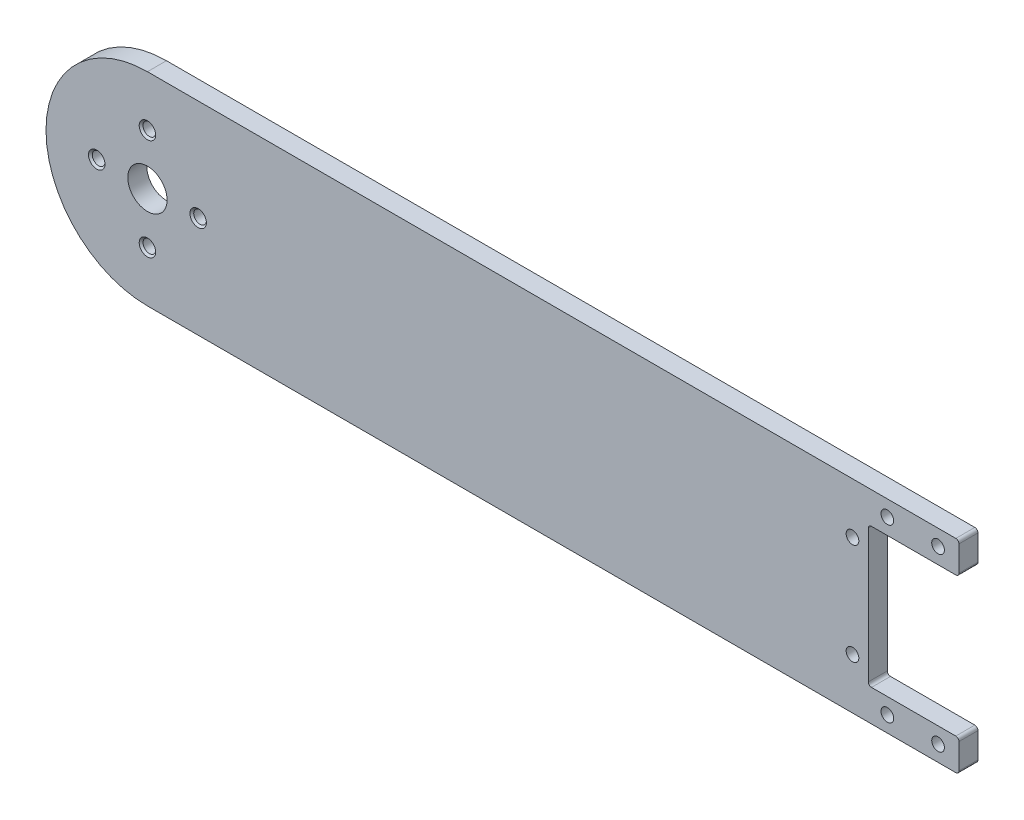
SolidWorks part; units mm, degrees
material "ABS"
ref_plane "Ön Düzlem" through (0, 0, 0) normal (0, 0, 1) x (1, 0, 0)
ref_plane "Üst Düzlem" through (0, 0, 0) normal (0, 1, 0) x (1, 0, 0)
ref_plane "Sağ Düzlem" through (0, 0, 0) normal (1, 0, 0) x (0, 0, -1)
sketch "Çizim1" plane through (0, 0, 0) normal (0, 0, 1) x (1, 0, 0)
  line L0 (-61, -16) -> (59, -16)
  line L1 (-61, 16) -> (59, 16)
  line L3 (59, 16) -> (75, 16)
  line L4 (59, 16) -> (59, -16)
  line L5 (59, -16) -> (75, -16)
  line L6 (75, 16) -> (75, -16)
  arc A0 (59, 16) -> (75, 0) centre (59, 0) cw
  arc A1 (-61, 16) -> (-77, 0) centre (-61, 0) ccw
  circle A2 centre (-61, 0) radius 16
  circle A3 centre (59, 0) radius 16
  point P0 (0, 0)
  dimension "D3" = 16
  dimension "D4" = 32
  dimension "D5" = 32
  dimension "D7" = 16
  dimension "D8" = 61
  dimension "D2" = 120
  dimension "D6" = 120
  dimension "D9" = 16
  dimension "D10" = 32
  dimension "D11" = 16
  dimension "D12" = 152
extrude "Yükseklik-Ekstrüzyon1" add sketch "Çizim1" along normal blind 3 contours A3 L1 A2 L0 | A0 A3 | L4 L3 L6 L5
sketch "Çizim2" plane through (0, 0, 3) normal (0, 0, 1) x (1, 0, 0)
  circle A0 centre (-61, 0) radius 8 construction
  circle A1 centre (-61, 0) radius 3.1
  point P4 (-61, 8)
  point P5 (-53, 0)
  point P6 (-61, -8)
  point P7 (-69, 0)
  dimension "D1" = 16
  dimension "D2" = 6.2
extrude "Kes-Ekstrüzyon1" cut sketch "Çizim2" against normal through all
hole_wizard "M2 Düz Başlı Makine Vidası İçin Havşa1" positions "3B Çizim1" profile "Çizim7" countersink size "M2" standard "ANSI Metrik" end condition through all
sketch3d "3B Çizim1"
  point P0 (-61, 8, 3)
  point P3 (-53, 0, 3)
  point P6 (-61, -8, 3)
  point P9 (-69, 0, 3)
sketch "Çizim7" plane through (-61, 8, 3) normal (1, 0, 0) x (0, -1, 0)
  line L0 (0, 0) -> (0, 3)
  line L1 (0, 3) -> (1, 3)
  line L2 (1, 3) -> (1, 0.3)
  line L3 (1, 0.3) -> (1.3, 0)
  line L5 (1.3, 0) -> (0, 0)
  line L6 (-1, 0.3) -> (-1.3, 0) construction
  line L11 (0, -6.35) -> (0, 107.95) construction
  dimension "Thru Hole Dia." = 2
  dimension "Thru Hole Depth" = 3
  dimension "Near C'Sink Dia." = 2.6
  dimension "Near C'Sink Angle" = 90
sketch "Çizim26" plane through (0, 0, 3) normal (0, 0, 1) x (1, 0, 0)
  line L0 (75, 16) -> (75, -16) construction
  line L1 (75, 11) -> (52.7, 11)
  line L2 (75, 11) -> (75, -11)
  line L3 (75, -11) -> (52.7, -11)
  line L4 (52.7, 11) -> (52.7, -11)
  line L5 (-61, -16) -> (75, -16) construction
  line L6 (-61, 16) -> (75, 16) construction
  point P8 (71.7, 13.5)
  point P9 (63.7, 13.5)
  point P10 (55.7, 13.5)
  point P11 (50.2, 8)
  point P12 (50.2, -8)
  point P13 (55.7, -13.5)
  point P14 (63.7, -13.5)
  point P15 (71.7, -13.5)
  dimension "D1" = 22.3
  dimension "D2" = 22
  dimension "D3" = 5
  dimension "D4" = 8
  dimension "D5" = 8
  dimension "D6" = 8
  dimension "D7" = 8
  dimension "D8" = 2.5
  dimension "D9" = 2.5
  dimension "D10" = 3.3
  dimension "D11" = 3.3
  dimension "D12" = 8
  dimension "D13" = 2.5
  dimension "D14" = 2.5
  dimension "D15" = 8
extrude "Kes-Ekstrüzyon4" cut sketch "Çizim26" against normal through all
sketch "Vida Del. Ref" plane through (0, 0, 0) normal (0, 0, -1) x (-1, 0, 0)
  point P0 (-71.7, 13.5)
  point P1 (-63.7, 13.5)
  point P3 (-55.7, 13.5)
  point P5 (-50.2, 8)
  point P7 (-50.2, -8)
  point P9 (-55.7, -13.5)
  point P11 (-63.7, -13.5)
  point P13 (-71.7, -13.5)
hole_wizard "M2 Düz Başlı Makine Vidası İçin Havşa2" positions "3B Çizim4" profile "Çizim32" countersink size "M2" standard "ANSI Metrik" end condition through all
sketch3d "3B Çizim4"
  point P0 (71.7, 13.5, 0)
  point P3 (63.7, 13.5, 0)
  point P6 (55.7, 13.5, 0)
  point P9 (50.2, 8, 0)
  point P12 (50.2, -8, 0)
  point P15 (55.7, -13.5, 0)
  point P18 (63.7, -13.5, 0)
  point P21 (71.7, -13.5, 0)
sketch "Çizim32" plane through (71.7, 13.5, 0) normal (1, 0, 0) x (0, 1, 0)
  line L0 (0, 0) -> (0, 3)
  line L1 (0, 3) -> (1, 3)
  line L2 (1, 3) -> (1, 0.3)
  line L3 (1, 0.3) -> (1.3, 0)
  line L5 (1.3, 0) -> (0, 0)
  line L6 (-1, 0.3) -> (-1.3, 0) construction
  line L11 (0, -6.35) -> (0, 107.95) construction
  dimension "Thru Hole Dia." = 2
  dimension "Thru Hole Depth" = 3
  dimension "Near C'Sink Dia." = 2.6
  dimension "Near C'Sink Angle" = 90
sketch "Çizim33" plane through (0, 0, 0) normal (0, 0, -1) x (-1, 0, 0)
  line L0 (61, -16) -> (-75, -16) construction
  line L1 (-75, 16) -> (-67, 16)
  line L2 (-75, 16) -> (-75, -16)
  line L3 (-75, -16) -> (-67, -16)
  line L4 (-67, 16) -> (-67, -16)
  dimension "D1" = 8
extrude "Kes-Ekstrüzyon5" cut sketch "Çizim33" against normal blind 10
fillet "Radyus1" radius 0.5 6 edges at (52.7, 11, 1.5) (52.7, -11, 1.5) (67, -16, 1.5) (67, -11, 1.5) (67, 11, 1.5) (67, 16, 1.5)
